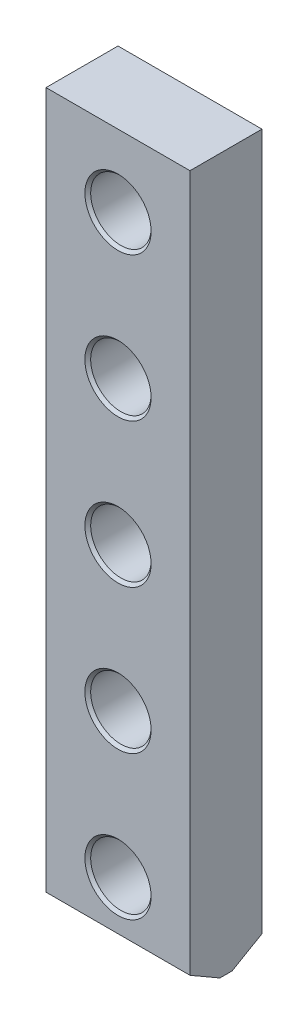
SolidWorks part; units mm, degrees
material "Простая углеродистая сталь"
ref_plane "Спереди" through (0, 0, 0) normal (0, 0, 1) x (1, 0, 0)
ref_plane "Сверху" through (0, 0, 0) normal (0, 1, 0) x (1, 0, 0)
ref_plane "Справа" through (0, 0, 0) normal (1, 0, 0) x (0, 0, -1)
sketch "Эскиз1" plane through (0, 0, 0) normal (0, 0, 1) x (1, 0, 0)
  line L1 (0, 0) -> (50, 0)
  line L2 (0, 0) -> (0, 248)
  line L3 (0, 248) -> (50, 248)
  line L4 (50, 0) -> (50, 248)
  point P5 (25, 248)
  dimension "D1" = 248
  dimension "D2" = 50
extrude "Бобышка-Вытянуть1" add sketch "Эскиз1" along normal blind 25
sketch "Эскиз2" plane through (0, 0, 25) normal (0, 0, 1) x (1, 0, 0)
  line L0 (0, 0) -> (50, 0) construction
  line L1 (50, 0) -> (50, 248) construction
  circle A0 centre (25, 23) radius 10.5
  circle A1 centre (25, 73) radius 10.5
  circle A2 centre (25, 123) radius 10.5
  circle A3 centre (25, 173) radius 10.5
  circle A4 centre (25, 223) radius 10.5
  dimension "D1" = 5
  dimension "D2" = 23
  dimension "D3" = 25
  dimension "D4" = 21
extrude "Вырез-Вытянуть1" cut sketch "Эскиз2" against normal through all
chamfer "Фаска1" distance 6 angle 60 1 edges at (25, 0, 0)
chamfer "Фаска2" distance 6 angle 60 1 edges at (25, 0, 25)
chamfer "Фаска3" distance 1 angle 45 10 edges at (35.5, 223, 0) (35.5, 23, 0) (35.5, 73, 0) (35.5, 123, 0) (35.5, 173, 0) (35.5, 23, 25) (35.5, 73, 25) (35.5, 223, 25) (35.5, 173, 25) (35.5, 123, 25)
